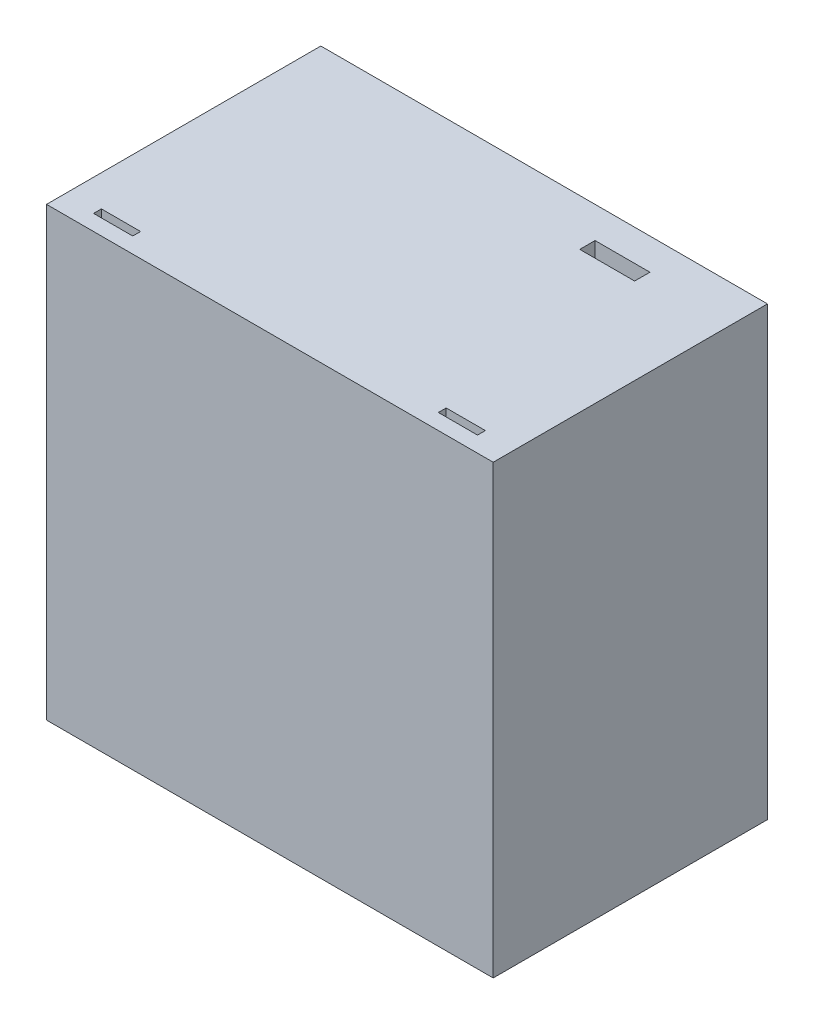
SolidWorks part; units mm, degrees
ref_plane "Front Plane" through (0, 0, 0) normal (0, 0, 1) x (1, 0, 0)
ref_plane "Top Plane" through (0, 0, 0) normal (0, 1, 0) x (1, 0, 0)
ref_plane "Right Plane" through (0, 0, 0) normal (1, 0, 0) x (0, 0, -1)
sketch "Sketch2" plane through (0, 0, 0) normal (0, 0, 1) x (1, 0, 0)
  line L5 (-34.233, 27.7621) -> (22.767, 27.7621)
  line L6 (-34.233, 27.7621) -> (-34.233, -29.2379)
  line L7 (-34.233, -29.2379) -> (22.767, -29.2379)
  line L8 (22.767, 27.7621) -> (22.767, -29.2379)
  dimension "D1" = 57
  dimension "D2" = 57
extrude "Boss-Extrude1" add sketch "Sketch2" along normal blind 35
sketch "Sketch3" plane through (0, 27.7621, 0) normal (0, 1, 0) x (1, 0, 0)
  line L1 (-30.233, -32) -> (-25.233, -32)
  line L2 (-30.233, -32) -> (-30.233, -33)
  line L3 (-30.233, -33) -> (-25.233, -33)
  line L4 (-25.233, -32) -> (-25.233, -33)
  line L5 (13.767, -32) -> (18.767, -32)
  line L6 (13.767, -32) -> (13.767, -33)
  line L7 (13.767, -33) -> (18.767, -33)
  line L8 (18.767, -32) -> (18.767, -33)
  line L9 (-34.233, -35) -> (-34.233, 0) construction
  line L10 (22.767, -35) -> (22.767, 0) construction
  line L11 (22.767, 0) -> (-34.233, 0) construction
  point P8 (-25.233, -32.5)
  point P9 (13.767, -32.5)
  dimension "D1" = 1
  dimension "D3" = 5
  dimension "D4" = 4
  dimension "D5" = 4
  dimension "D6" = 32
extrude "Cut-Extrude1" cut sketch "Sketch3" against normal blind 60
sketch "Sketch4" plane through (0, 0, 0) normal (0, 0, -1) x (-1, 0, 0)
  line L1 (-19.017, 24.0121) -> (30.483, 24.0121)
  line L2 (-19.017, 24.0121) -> (-19.017, -25.4879)
  line L3 (-19.017, -25.4879) -> (30.483, -25.4879)
  line L4 (30.483, 24.0121) -> (30.483, -25.4879)
  line L6 (34.233, -29.2379) -> (-22.767, -29.2379) construction
  line L7 (-22.767, -29.2379) -> (-22.767, 27.7621) construction
  dimension "D1" = 49.5
  dimension "D2" = 3.75
  dimension "D3" = 3.75
  dimension "D4" = 49.5
extrude "Cut-Extrude2" cut sketch "Sketch4" against normal blind 28
sketch "Sketch5" plane through (0, -25.4879, 0) normal (0, 1, 0) x (1, 0, 0)
  line L0 (-30.483, -28) -> (-30.483, 0) construction
  line L3 (19.017, 0) -> (-30.483, 0) construction
  line L5 (2.767, -12) -> (2.767, 0)
  line L6 (2.767, 0) -> (-14.233, 0)
  line L7 (-14.233, 0) -> (-14.233, -12)
  arc A0 (-14.233, -12) -> (2.767, -12) centre (-5.733, -12) ccw
  dimension "D3" = 8.5
  dimension "D1" = 24.75
  dimension "D2" = 12
extrude "Cut-Extrude4" cut sketch "Sketch5" against normal blind 5
sketch "Sketch7" plane through (-30.483, 0, 0) normal (1, 0, 0) x (0, 0, -1)
  line L0 (-28, -25.4879) -> (0, -25.4879) construction
  line L2 (0, -25.4879) -> (0, 24.0121) construction
  line L3 (-12, -9.2379) -> (0, -9.2379)
  line L4 (0, -9.2379) -> (0, 7.7621)
  line L8 (0, 7.7621) -> (-12, 7.7621)
  arc A1 (-12, 7.7621) -> (-12, -9.2379) centre (-12, -0.7379) ccw
  dimension "D3" = 8.5
  dimension "D1" = 24.75
  dimension "D2" = 12
extrude "Cut-Extrude5" cut sketch "Sketch7" against normal blind 10
sketch "Sketch13" plane through (0, 27.7621, 0) normal (0, 1, 0) x (1, 0, 0)
  line L1 (4.767, -4) -> (11.767, -4)
  line L2 (4.767, -4) -> (4.767, -5.9526)
  line L3 (4.767, -5.9526) -> (11.767, -5.9526)
  line L4 (11.767, -4) -> (11.767, -5.9526)
  line L6 (22.767, -35) -> (22.767, 0) construction
  line L7 (-34.233, -35) -> (-34.233, 0) construction
  line L8 (22.767, 0) -> (-34.233, 0) construction
  dimension "D1" = 11
  dimension "D2" = 39
  dimension "D3" = 4
extrude "Cut-Extrude8" cut sketch "Sketch13" against normal blind 12
